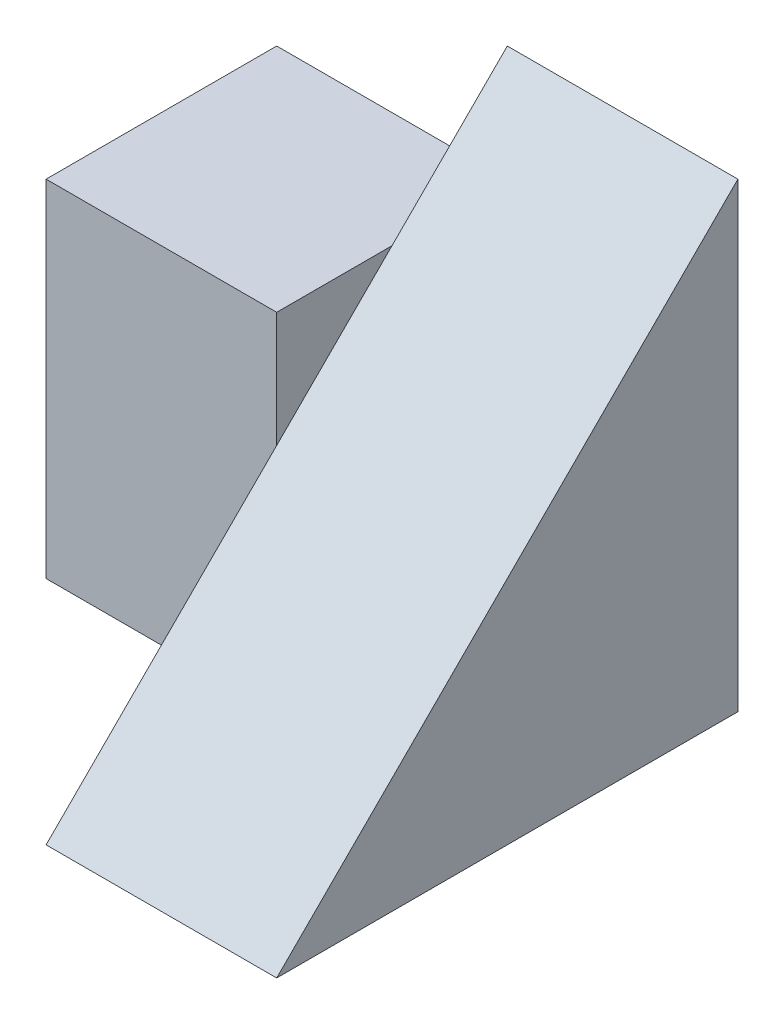
SolidWorks part; units mm, degrees
ref_plane "Front Plane" through (0, 0, 0) normal (0, 0, 1) x (1, 0, 0)
ref_plane "Top Plane" through (0, 0, 0) normal (0, 1, 0) x (1, 0, 0)
ref_plane "Right Plane" through (0, 0, 0) normal (1, 0, 0) x (0, 0, -1)
sketch "Sketch1" plane through (0, 0, 0) normal (1, 0, 0) x (0, 0, -1)
  line L1 (0, 0) -> (4, 0)
  line L2 (0, 0) -> (0, 4)
  line L3 (0, 4) -> (4, 4)
  line L4 (4, 0) -> (4, 4)
  dimension "D1" = 4
  dimension "D2" = 4
extrude "Boss-Extrude1" add sketch "Sketch1" along normal blind 2
sketch "Sketch2" plane through (0, 0, 0) normal (-1, 0, 0) x (0, 0, 1)
  line L1 (-4, 0) -> (-2, 0)
  line L2 (-4, 0) -> (-4, 3)
  line L3 (-4, 3) -> (-2, 3)
  line L4 (-2, 0) -> (-2, 3)
  dimension "D1" = 3
  dimension "D2" = 2
extrude "Boss-Extrude2" add sketch "Sketch2" along normal blind 2
sketch "Sketch3" plane through (2, 0, 0) normal (1, 0, 0) x (0, 0, -1)
  line L0 (4, 4) -> (0, 0)
  line L1 (0, 0) -> (0, 4)
  line L2 (0, 4) -> (4, 4)
extrude "Cut-Extrude1" cut sketch "Sketch3" against normal blind 2
